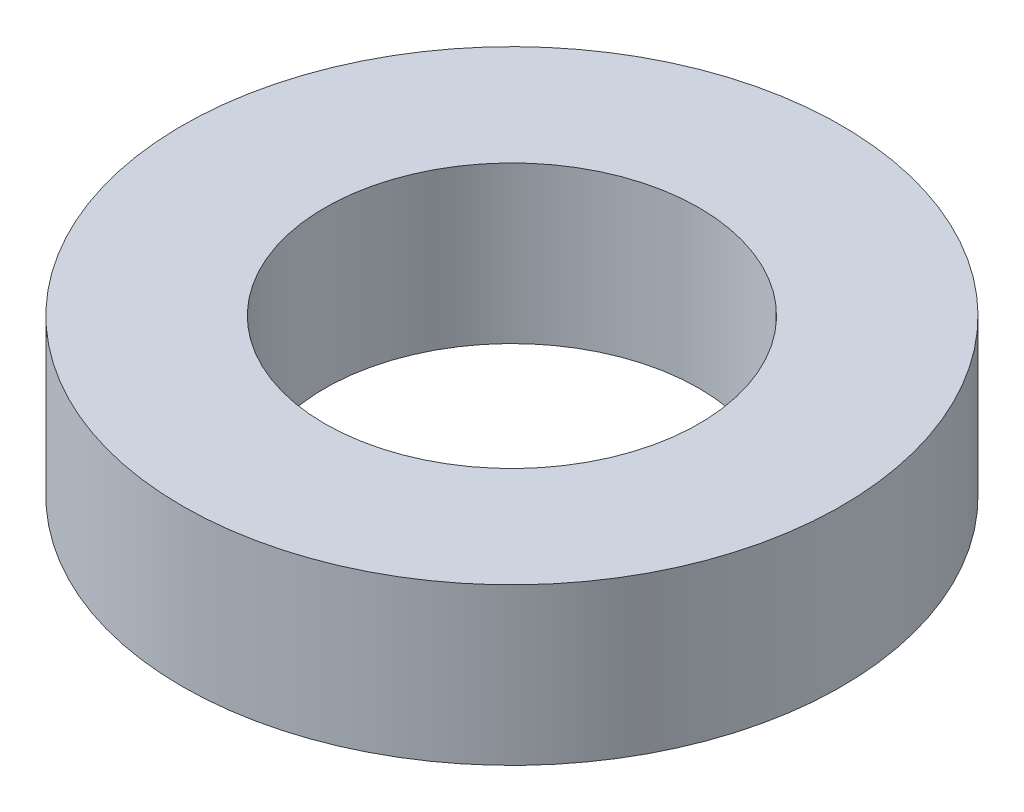
SolidWorks part; units mm, degrees
ref_plane "Front Plane" through (0, 0, 0) normal (0, 0, 1) x (1, 0, 0)
ref_plane "Top Plane" through (0, 0, 0) normal (0, 1, 0) x (1, 0, 0)
ref_plane "Right Plane" through (0, 0, 0) normal (1, 0, 0) x (0, 0, -1)
sketch "Sketch1" plane through (0, 0, 0) normal (0, 1, 0) x (1, 0, 0)
  circle A0 centre (0, 0) radius 14.986
  circle A1 centre (0, 0) radius 8.509
  dimension "D1" = 29.972
  dimension "D2" = 17.018
extrude "Boss-Extrude1" add sketch "Sketch1" along normal blind 7.112
